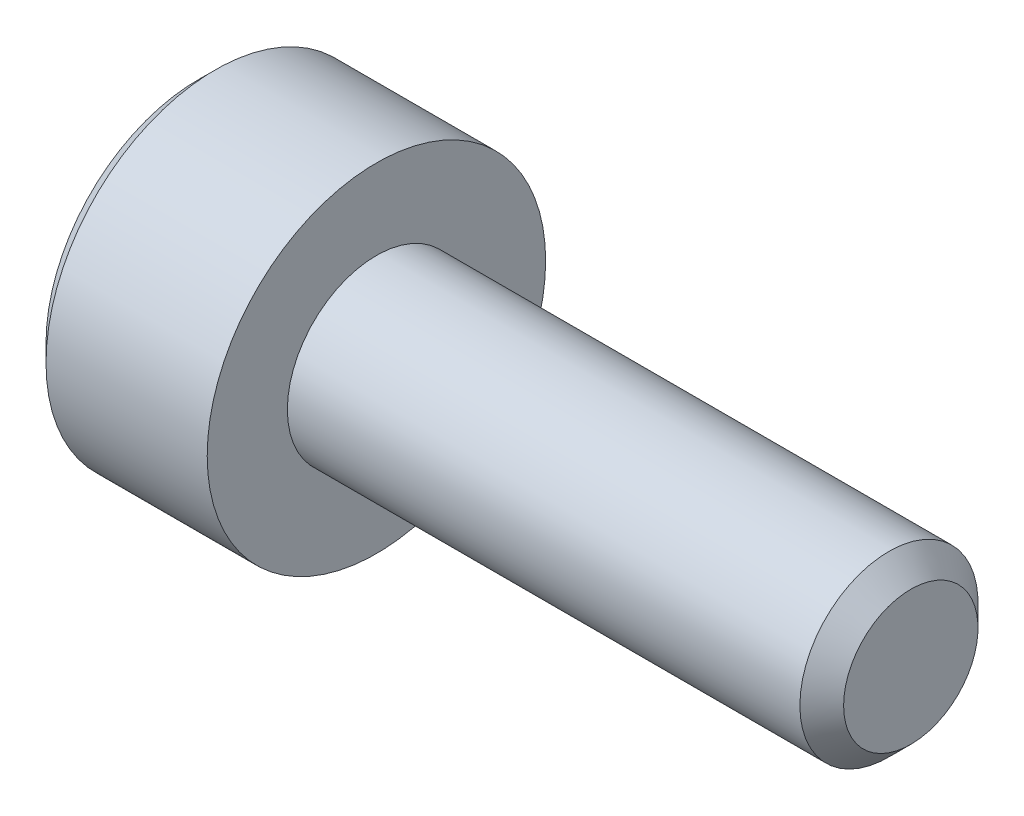
SolidWorks part; units mm, degrees
material "AISI 304"
ref_plane "正面" through (0, 0, 0) normal (0, 0, 1) x (1, 0, 0)
ref_plane "平面" through (0, 0, 0) normal (0, 1, 0) x (1, 0, 0)
ref_plane "右側面" through (0, 0, 0) normal (1, 0, 0) x (0, 0, -1)
ref_plane "Plane1" through (0, 0, 0) normal (0, 0, 1) x (1, 0, 0)
sketch "Sketch1" plane through (0, 0, 0) normal (0, 0, 1) x (1, 0, 0)
  line L0 (-2, 0) -> (-2, 1.71)
  line L1 (-2, 1.71) -> (-1.81, 1.9)
  line L2 (-1.81, 1.9) -> (0, 1.9)
  line L3 (0, 1.9) -> (0, 1)
  line L4 (0, 1) -> (5.7545, 1)
  line L5 (5.7545, 1) -> (6, 0.7545)
  line L6 (6, 0.7545) -> (6, 0)
  line L7 (6, 0) -> (-2, 0)
  line L8 (6, 0) -> (-2, 0) construction
revolve "Revolve1" add sketch "Sketch1" angle 360 about L8
cosmetic thread "Cosmetic Thread1" parameters "D1"=5.5748, "D2"=1.509
ref_plane "Plane2" through (-2, 0, 0) normal (1, 0, 0) x (0, 0, -1)
sketch "Sketch2" plane through (-2, 0, 0) normal (1, 0, 0) x (0, 0, -1)
  line L0 (-0.75, -0.433) -> (0, -0.866)
  line L1 (0, -0.866) -> (0.75, -0.433)
  line L2 (0.75, -0.433) -> (0.75, 0.433)
  line L3 (0.75, 0.433) -> (0, 0.866)
  line L4 (0, 0.866) -> (-0.75, 0.433)
  line L5 (-0.75, 0.433) -> (-0.75, -0.433)
extrude "Cut-Extrude1" cut sketch "Sketch2" along normal blind 0.8
